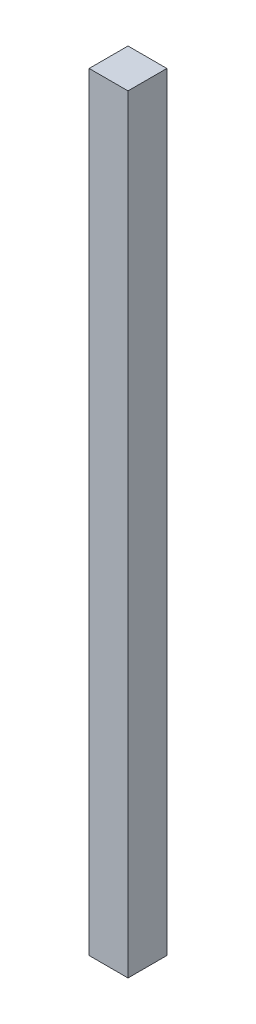
SolidWorks part; units mm, degrees
ref_plane "Plan de face" through (0, 0, 0) normal (0, 0, 1) x (1, 0, 0)
ref_plane "Plan de dessus" through (0, 0, 0) normal (0, 1, 0) x (1, 0, 0)
ref_plane "Plan de droite" through (0, 0, 0) normal (1, 0, 0) x (0, 0, -1)
sketch "Esquisse1" plane through (0, 0, 0) normal (0, 0, 1) x (1, 0, 0)
  line L1 (-81.3222, 77.6389) -> (-68.3222, 77.6389)
  line L2 (-81.3222, 77.6389) -> (-81.3222, -179.3611)
  line L3 (-81.3222, -179.3611) -> (-68.3222, -179.3611)
  line L4 (-68.3222, 77.6389) -> (-68.3222, -179.3611)
  dimension "D1" = 13
  dimension "D2" = 257
extrude "Boss.-Extru.1" add sketch "Esquisse1" along normal blind 13 contours L2 L3 L4 L1
equation "\"EpaisseurPlaque\"= 3"
equation "\"ProfondeurBoite\"=460"
equation "\"LongueurSyphon\"=270"
equation "\"LargeurSyphon\"=120"
equation "\"HauteurCoteDroit\"= 490"
equation "\"HauteurCoteGauche\"= 540"
equation "\"HauteurSolSyphon\"= 300"
equation "\"HauteurSyphon\"=\"HauteurCoteGauche\"-\"HauteurSolSyphon\""
equation "\"LargeurDroite\"=10"
equation "\"LargeurGauche\"=150"
equation "\"LargeurBoite\"= \"LargeurDroite\" + \"LargeurGauche\" + \"LargeurSyphon\""
equation "\"D2@Esquisse1\"=\"LongueurSyphon\" -  10 - 3"
